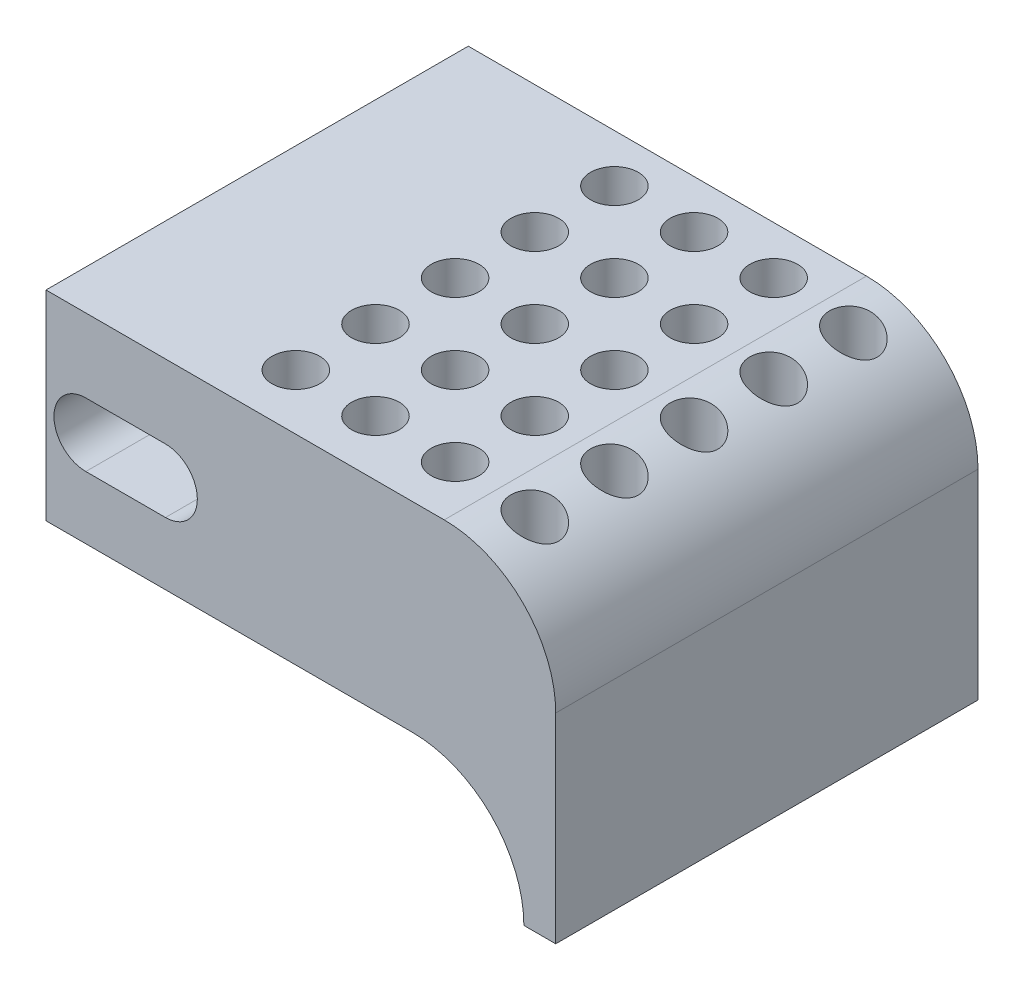
SolidWorks part; units mm, degrees
ref_plane "Plan de face" through (0, 0, 0) normal (0, 0, 1) x (1, 0, 0)
ref_plane "Plan de dessus" through (0, 0, 0) normal (0, 1, 0) x (1, 0, 0)
ref_plane "Plan de droite" through (0, 0, 0) normal (1, 0, 0) x (0, 0, -1)
sketch "Esquisse1" plane through (0, 0, 0) normal (0, 0, 1) x (1, 0, 0)
  line L0 (30, 12.55) -> (30, 0) construction
  line L1 (0, 0) -> (23, 0)
  line L2 (0, 0) -> (0, 12.55)
  line L3 (0, 12.55) -> (32, 12.55)
  line L4 (32, -2.95) -> (32, 12.55)
  line L5 (23, 12.55) -> (23, 0) construction
  line L6 (23, 0) -> (23, -7) construction
  line L7 (23, -7) -> (30, -7) construction
  line L8 (30, -7) -> (32, -7)
  line L9 (32, -7) -> (32, -2.95)
  line L10 (2.5, 5.9293) -> (7.5, 5.9293) construction
  line L11 (2.5, 7.9293) -> (7.5, 7.9293)
  line L12 (2.5, 3.9293) -> (7.5, 3.9293)
  line L13 (0, 6.275) -> (32, 4.8) construction
  arc A0 (23, 0) -> (30, -7) centre (23, -7) cw
  arc A1 (2.5, 7.9293) -> (2.5, 3.9293) centre (2.5, 5.9293) ccw
  arc A2 (7.5, 3.9293) -> (7.5, 7.9293) centre (7.5, 5.9293) ccw
  point P15 (5, 5.9293)
  dimension "D5" = 5
  dimension "D1" = 12.55
  dimension "D2" = 32
  dimension "D3" = 2
  dimension "D4" = 7
  dimension "D6" = 2.5
  dimension "D7" = 7
extrude "Boss.-Extru.1" add sketch "Esquisse1" along normal blind 26.51
fillet "Congé1" radius 7 1 edges at (32, 12.55, 13.255)
sketch "Esquisse2" plane through (0, 0, 0) normal (0, -1, 0) x (1, 0, 0)
  circle A0 centre (12.1937, 3.0194) radius 1.5
  circle A1 centre (17.1937, 3.0194) radius 1.5
  circle A2 centre (22.1937, 3.0194) radius 1.5
  circle A3 centre (17.1937, 8.0194) radius 1.5
  circle A4 centre (22.1937, 8.0194) radius 1.5
  circle A5 centre (17.1937, 13.0194) radius 1.5
  circle A6 centre (22.1937, 13.0194) radius 1.5
  circle A7 centre (17.1937, 18.0194) radius 1.5
  circle A8 centre (22.1937, 18.0194) radius 1.5
  circle A9 centre (17.1937, 23.0194) radius 1.5
  circle A10 centre (22.1937, 23.0194) radius 1.5
  circle A11 centre (12.1937, 8.0194) radius 1.5
  circle A12 centre (12.1937, 13.0194) radius 1.5
  circle A13 centre (12.1937, 18.0194) radius 1.5
  circle A14 centre (12.1937, 23.0194) radius 1.5
  circle A15 centre (27.1937, 3.0194) radius 1.5
  circle A16 centre (27.1937, 8.0194) radius 1.5
  circle A17 centre (27.1937, 13.0194) radius 1.5
  circle A18 centre (27.1937, 18.0194) radius 1.5
  circle A19 centre (27.1937, 23.0194) radius 1.5
  dimension "D1" = 5
  dimension "D2" = 4
extrude "Enlèv. mat.-Extru.2" cut sketch "Esquisse2" against normal blind 20 and the other way blind 10
